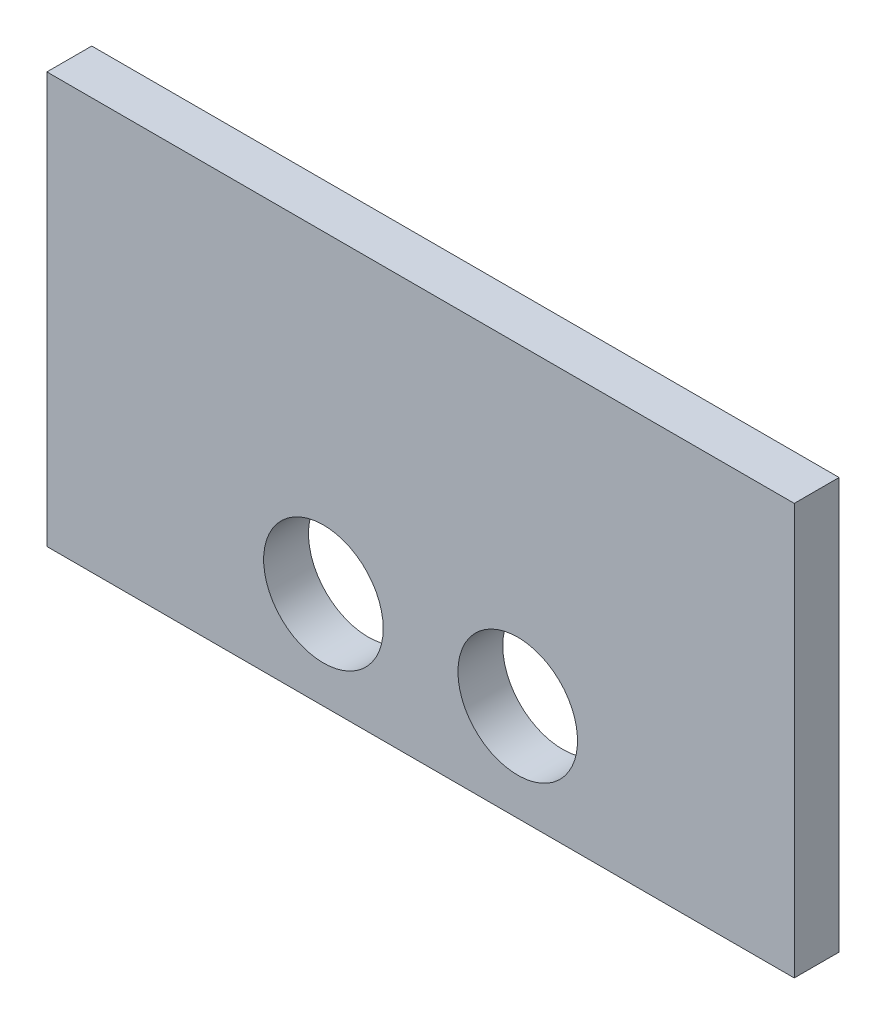
SolidWorks part; units mm, degrees
ref_plane "정면" through (0, 0, 0) normal (0, 0, 1) x (1, 0, 0)
ref_plane "윗면" through (0, 0, 0) normal (0, 1, 0) x (1, 0, 0)
ref_plane "우측면" through (0, 0, 0) normal (1, 0, 0) x (0, 0, -1)
sketch "Sketch1" plane through (0, 0, 0) normal (0, 0, 1) x (1, 0, 0)
  line L0 (0, -47.122) -> (0, 62.6191) construction
  line L1 (50, 46.4012) -> (-50, 46.4012)
  line L2 (-50, 46.4012) -> (-50, -8.5988)
  line L3 (-50, -8.5988) -> (50, -8.5988)
  line L4 (50, 46.4012) -> (50, -8.5988)
  point P8 (0, -8.5988)
  point P9 (0, 46.4012)
  dimension "D1" = 50
  dimension "D2" = 55
extrude "Boss-Extrude1" add sketch "Sketch1" along normal blind 6
sketch "Sketch2" plane through (0, 0, 6) normal (0, 0, 1) x (1, 0, 0)
  line L0 (0, -16.3454) -> (0, 57.3935) construction
  line L3 (-50, -8.5988) -> (50, -8.5988) construction
  circle A0 centre (-13, 4.4012) radius 8
  circle A1 centre (13, 4.4012) radius 8
  point P5 (0, 0)
  point P7 (-15.2651, -8.5988)
  point P8 (-23.988, -8.5988)
  dimension "D1" = 13
  dimension "D2" = 13
extrude "Cut-Extrude1" cut sketch "Sketch2" against normal blind 6
